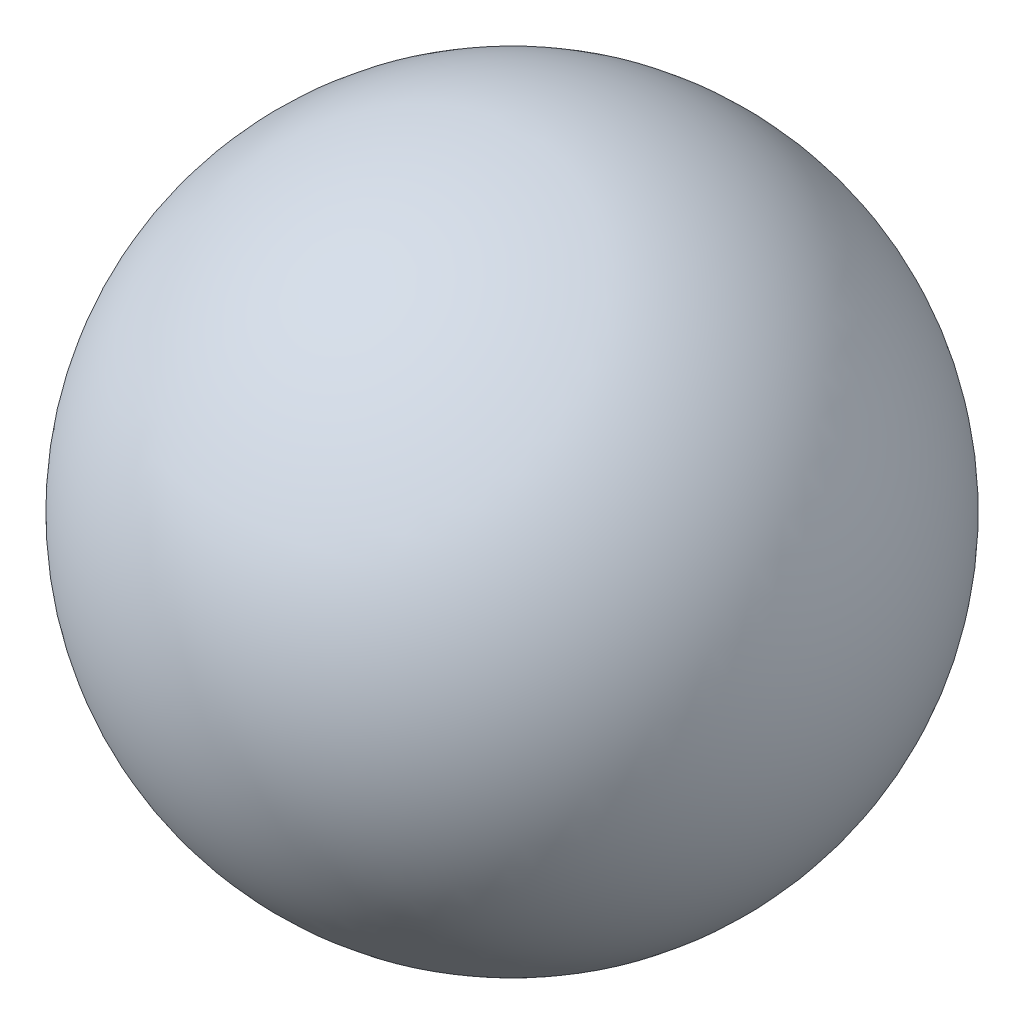
SolidWorks part; units mm, degrees
ref_plane "Front Plane" through (0, 0, 0) normal (0, 0, 1) x (1, 0, 0)
ref_plane "Top Plane" through (0, 0, 0) normal (0, 1, 0) x (1, 0, 0)
ref_plane "Right Plane" through (0, 0, 0) normal (1, 0, 0) x (0, 0, -1)
sketch "Sketch1" plane through (0, 0, 0) normal (0, 0, 1) x (1, 0, 0)
  line L0 (0, 119.8563) -> (0, -119.8563)
  arc A0 (0, -119.8563) -> (0, 119.8563) centre (0, 0) ccw
  point P4 (0, 0)
  dimension "D1" = 239.7125
revolve "Revolve1" add sketch "Sketch1" angle 360 about L0
ref_plane "Plane1" through (0, 119.8563, 0) normal (0, 1, 0) x (1, 0, 0)
sketch "Sketch2" plane through (0, 119.8563, 0) normal (0, 1, 0) x (1, 0, 0)
  line L0 (0, 152.4) -> (0, -152.4) construction
  line L1 (-76.2, 0) -> (76.2, 0) construction
  line L2 (0, 247.65) -> (0, -247.65) construction
  circle A0 centre (0, 152.4) radius 95.25
  circle A1 centre (0, -152.4) radius 95.25
  arc A2 (-95.25, 152.4) -> (-95.25, -152.4) centre (-695.325, 0) cw
  arc A3 (95.25, 152.4) -> (95.25, -152.4) centre (695.325, 0) ccw
  circle A4 centre (0, 152.4) radius 90.4875
  circle A5 centre (0, -152.4) radius 90.4875
  arc A6 (-90.4875, 152.4) -> (-90.4875, -152.4) centre (-695.325, 0) cw
  arc A7 (90.4875, 152.4) -> (90.4875, -152.4) centre (695.325, 0) ccw
  point P10 (0, 0)
  dimension "D1" = 190.5
  dimension "D4" = 4.7625
  dimension "D2" = 152.4
  dimension "D3" = 152.4
  dimension "D5" = 495.3
sketch "Sketch3" plane through (0, 119.8563, 0) normal (0, 1, 0) x (1, 0, 0)
  arc A0 (95.25, 152.4) -> (95.25, -152.4) centre (695.325, 0) ccw construction
  circle A1 centre (0, -152.4) radius 95.25
  arc A2 (-86.518, -112.5604) -> (86.518, -112.5604) centre (0, -152.4) ccw
  circle A3 centre (0, 152.4) radius 95.25
  arc A4 (86.518, 112.5604) -> (-86.518, 112.5604) centre (0, 152.4) ccw
  arc A5 (-95.25, -152.4) -> (-95.25, 152.4) centre (-695.325, 0) ccw construction
  arc A6 (86.518, 112.5604) -> (86.518, -112.5604) centre (695.325, 0) ccw
  arc A7 (-86.518, -112.5604) -> (-86.518, 112.5604) centre (-695.325, 0) ccw
  arc A8 (90.4875, 152.4) -> (90.4875, -152.4) centre (695.325, 0) ccw construction
  circle A9 centre (0, -152.4) radius 90.4875 construction
  arc A10 (-90.4875, -152.4) -> (-90.4875, 152.4) centre (-695.325, 0) ccw construction
  circle A11 centre (0, 152.4) radius 90.4875 construction
  arc A12 (82.1921, 114.5524) -> (82.1921, -114.5524) centre (695.325, 0) ccw
  arc A13 (-82.1921, -114.5524) -> (82.1921, -114.5524) centre (0, -152.4) ccw
  arc A14 (-82.1921, -114.5524) -> (-82.1921, 114.5524) centre (-695.325, 0) ccw
  arc A15 (82.1921, 114.5524) -> (-82.1921, 114.5524) centre (0, 152.4) ccw
  dimension "D1" = 0
  dimension "D2" = 0
wrap "Wrap2" [suppressed] sketch "Sketch3" source sketch "Sketch3" thickness 1.5875 parameters "D1"=1.5875
